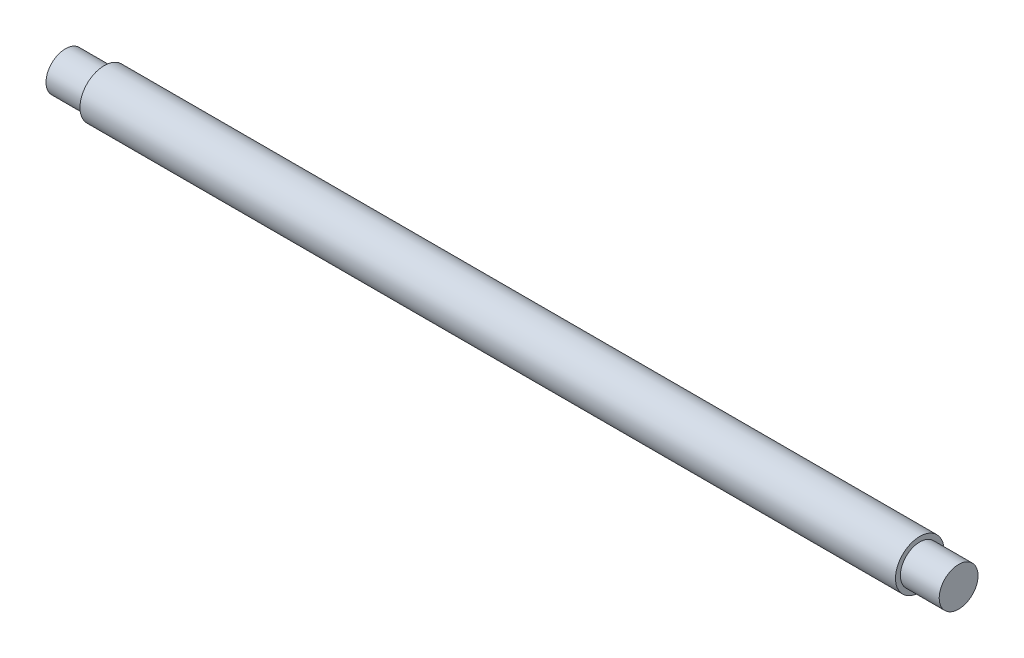
SolidWorks part; units mm, degrees
material "Plain Carbon Steel"
ref_plane "Front Plane" through (0, 0, 0) normal (0, 0, 1) x (1, 0, 0)
ref_plane "Top Plane" through (0, 0, 0) normal (0, 1, 0) x (1, 0, 0)
ref_plane "Right Plane" through (0, 0, 0) normal (1, 0, 0) x (0, 0, -1)
sketch "Sketch1" plane through (0, 0, 0) normal (1, 0, 0) x (0, 0, -1)
  circle A0 centre (0, 0) radius 12.5
  dimension "D1" = 25
extrude "Boss-Extrude1" add sketch "Sketch1" along normal mid plane 460
sketch "Sketch2" plane through (-230, 0, 0) normal (-1, 0, 0) x (0, 0, 1)
  circle A0 centre (0, 0) radius 10
  circle A1 centre (0, 0) radius 12.5
  dimension "D1" = 20
  dimension "D2" = 25
extrude "Cut-Extrude1" cut sketch "Sketch2" against normal blind 20
mirror "Mirror1" about plane through (0, 0, 0) normal (1, 0, 0) of "Cut-Extrude1"
